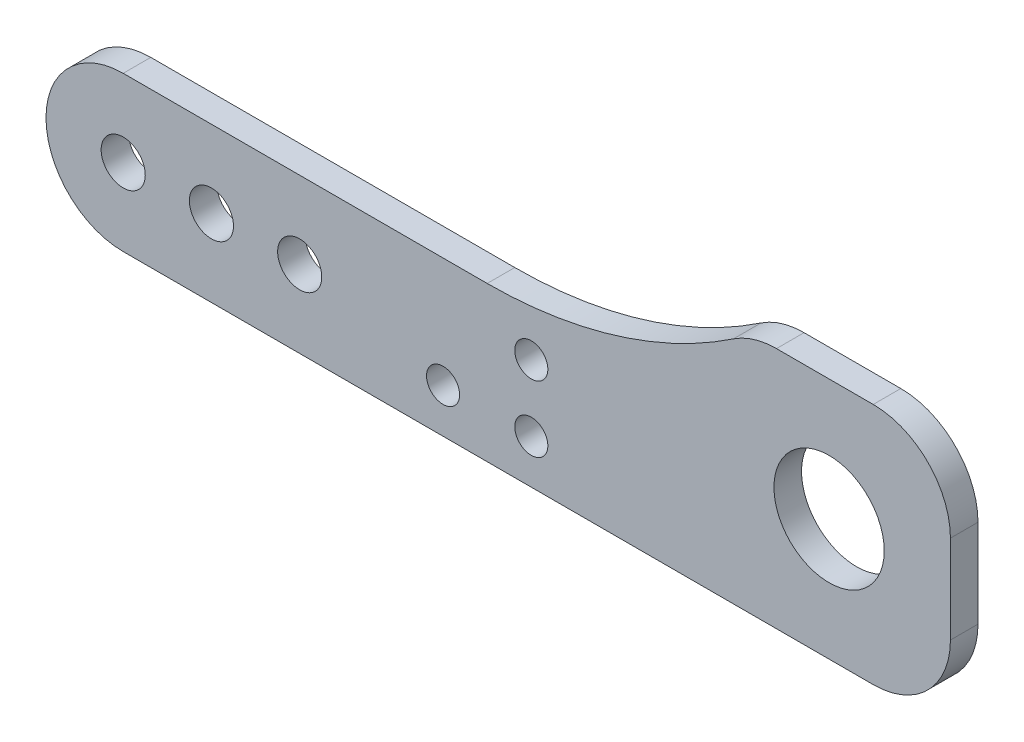
SolidWorks part; units mm, degrees
ref_plane "Front Plane" through (0, 0, 0) normal (0, 0, 1) x (1, 0, 0)
ref_plane "Top Plane" through (0, 0, 0) normal (0, 1, 0) x (1, 0, 0)
ref_plane "Right Plane" through (0, 0, 0) normal (1, 0, 0) x (0, 0, -1)
sketch "Sketch1" plane through (0, 0, 0) normal (0, 0, 1) x (1, 0, 0)
  line L0 (0, 7) -> (33, 7)
  line L1 (68, -7) -> (0, -7)
  line L5 (59.2298, 15) -> (68, 15)
  line L6 (75, 0) -> (75, 8)
  arc A1 (0, -7) -> (0, 7) centre (0, 0) cw
  arc A2 (33, 7) -> (55.3232, 13.8085) centre (33, 47) ccw
  arc A3 (68, -7) -> (75, 0) centre (68, 0) ccw
  arc A4 (68, 15) -> (75, 8) centre (68, 8) cw
  arc A5 (59.2298, 15) -> (55.3232, 13.8085) centre (59.2298, 8) ccw
  point P3 (75, -7)
  point P15 (75, 15)
  point P18 (57, 15)
  dimension "D2" = 7
  dimension "D4" = 40
  dimension "D1" = 7
  dimension "D3" = 22
  dimension "D5" = 18
  dimension "D6" = 75
extrude "Boss-Extrude1" add sketch "Sketch1" along normal blind 2.5
sketch "Sketch2" plane through (0, 0, 2.5) normal (0, 0, 1) x (1, 0, 0)
  line L0 (-7, 0) -> (-7, -7) construction
  line L6 (0, 0) -> (8, 0) construction
  line L7 (8, 0) -> (16, 0) construction
  line L8 (-7, -7) -> (0, -7) construction
  circle A0 centre (0, 0) radius 2
  circle A2 centre (8, 0) radius 2
  circle A5 centre (16, 0) radius 2
  arc A6 (0, 7) -> (0, -7) centre (0, 0) ccw construction
  dimension "D1" = 4
  dimension "D2" = 8
extrude "Cut-Extrude1" cut sketch "Sketch2" against normal up to surface (2.5 mm away) up to face at (47.7635, 5.6039, 0)
sketch "Sketch3" plane through (0, 0, 2.5) normal (0, 0, 1) x (1, 0, 0)
  line L0 (75, 0) -> (75, 8) construction
  line L2 (64, 4) -> (75, 4) construction
  line L3 (64, 4) -> (64, -7) construction
  line L4 (0, -7) -> (68, -7) construction
  circle A0 centre (64, 4) radius 5
  dimension "D1" = 10
extrude "Cut-Extrude2" cut sketch "Sketch3" against normal up to surface (2.5 mm away) up to face at (2, 0, 0)
hole_wizard "Ø3.0mm Dowel Hole2" positions "Sketch9" profile "Sketch10" hole size "Ø3.0" standard "ANSI Metric" end condition through all
sketch "Sketch9" plane through (0, 0, 0) normal (0, 0, -1) x (-1, 0, 0)
  line L2 (-75, 0) -> (-75, 8) construction
  line L3 (0, -7) -> (-68, -7) construction
  point P0 (-37, 3)
  point P3 (-37, -3)
  point P6 (-29, -3)
  dimension "D1" = 8
  dimension "D2" = 6
  dimension "D3" = 38
  dimension "D4" = 4
sketch "Sketch10" plane through (37, 3, 0) normal (1, 0, 0) x (0, 1, 0)
  line L0 (0, 0) -> (0, 2.5)
  line L1 (0, 2.5) -> (1.5, 2.5)
  line L2 (1.5, 2.5) -> (1.5, 0)
  line L5 (1.5, 0) -> (0, 0)
  line L11 (0, -6.35) -> (0, 107.95) construction
  dimension "Thru Hole Dia." = 3
  dimension "Thru Hole Depth" = 2.5
sketch "Sketch4" plane through (0, 0, 0) normal (0, 0, -1) x (-1, 0, 0)
  line L0 (0, -7) -> (-68, -7) construction
  line L1 (-49, -7) -> (-23, -7)
  line L2 (-49, -7) -> (-49, 10.3394)
  line L3 (-49, 10.3394) -> (-23, 10.3394)
  line L4 (-23, -7) -> (-23, 10.3394)
  line L5 (-75, 0) -> (-75, 8) construction
  arc A0 (-55.3232, 13.8085) -> (-33, 7) centre (-33, 47) ccw construction
  dimension "D1" = 26
  dimension "D2" = 26
extrude "Cut-Extrude3" [suppressed] cut sketch "Sketch4" against normal blind 1.6
